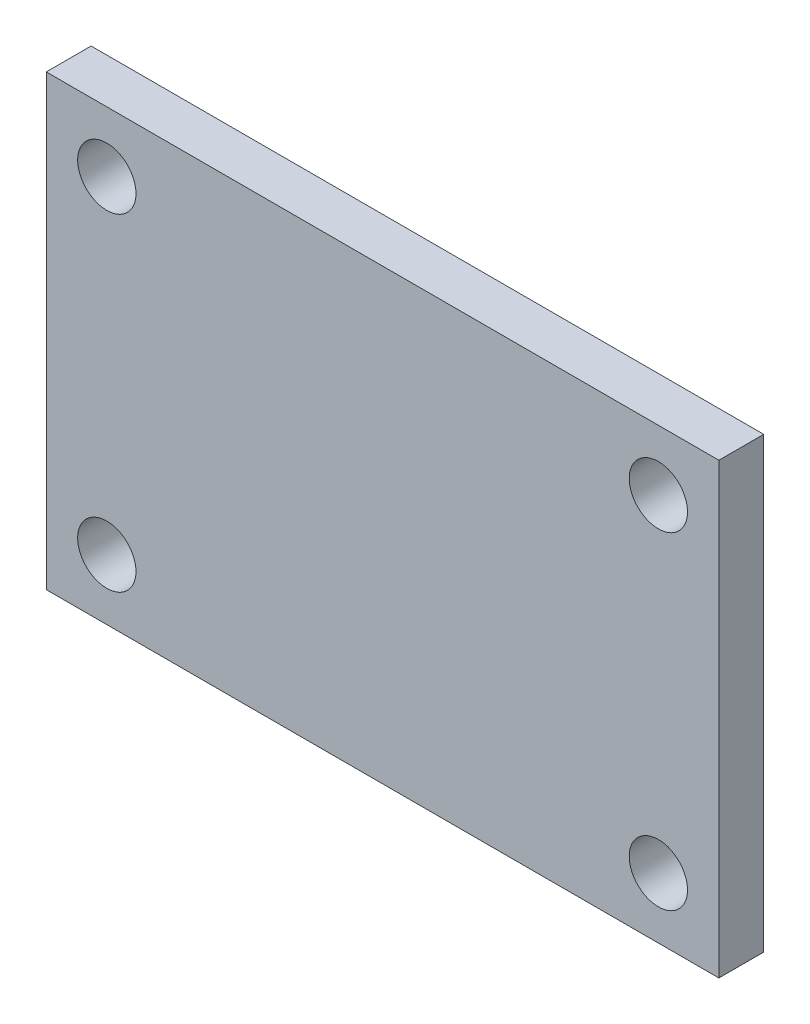
SolidWorks part; units mm, degrees
ref_plane "Plan de face" through (0, 0, 0) normal (0, 0, 1) x (1, 0, 0)
ref_plane "Plan de dessus" through (0, 0, 0) normal (0, 1, 0) x (1, 0, 0)
ref_plane "Plan de droite" through (0, 0, 0) normal (1, 0, 0) x (0, 0, -1)
sketch "Esquisse1" plane through (0, 0, 0) normal (0, 0, 1) x (1, 0, 0)
  line L0 (0, 0) -> (150, 0)
other "Elément mécano-soudé1"
ref_plane "Plan1" through (0, 0, 0) normal (1, 0, 0) x (0, 1, 0)
sketch "plat" plane through (0, 0, 0) normal (1, 0, 0) x (0, 1, 0)
  line L0 (-50, 0) -> (50, 0) construction
  line L1 (-50, 5) -> (50, 5)
  line L2 (-50, 5) -> (-50, -5)
  line L3 (-50, -5) -> (50, -5)
  line L4 (50, 5) -> (50, -5)
  line L5 (0, 5) -> (0, -5) construction
  point P8 (0, 0)
  dimension "B" = 100
  dimension "A" = 10
hole_wizard "Dégagement M121" positions "Esquisse3" profile "Esquisse2" hole size "M12" standard "ISO" end condition through all
sketch "Esquisse3" plane through (0, 0, 5) normal (0, 0, 1) x (1, 0, 0)
  line L0 (13.5, 36.5) -> (136.5, 36.5) construction
  line L1 (136.5, 36.5) -> (136.5, -36.5) construction
  line L2 (136.5, -36.5) -> (13.5, -36.5) construction
  line L3 (13.5, -36.5) -> (13.5, 36.5) construction
  line L6 (150, 50) -> (0, 50) construction
  line L7 (0, 50) -> (0, -50) construction
  point P0 (13.5, 36.5)
  point P1 (136.5, 36.5)
  point P3 (136.5, -36.5)
  point P5 (13.5, -36.5)
  point P16 (75, 36.5)
  point P19 (75, 50)
  point P20 (13.5, 0)
  point P23 (0, 0)
  dimension "D1" = 73
  dimension "D2" = 123
sketch "Esquisse2" plane through (13.5, 36.5, 5) normal (1, 0, 0) x (0, -1, 0)
  line L0 (0, 0) -> (0, 10)
  line L1 (0, 10) -> (6.5, 10)
  line L2 (6.5, 10) -> (6.5, 0)
  line L5 (6.5, 0) -> (0, 0)
  line L11 (0, -6.35) -> (0, 107.95) construction
  dimension "Diamètre du perçage jusqu'au prochain" = 13
  dimension "Profondeur du perçage jusqu'au prochain" = 10
